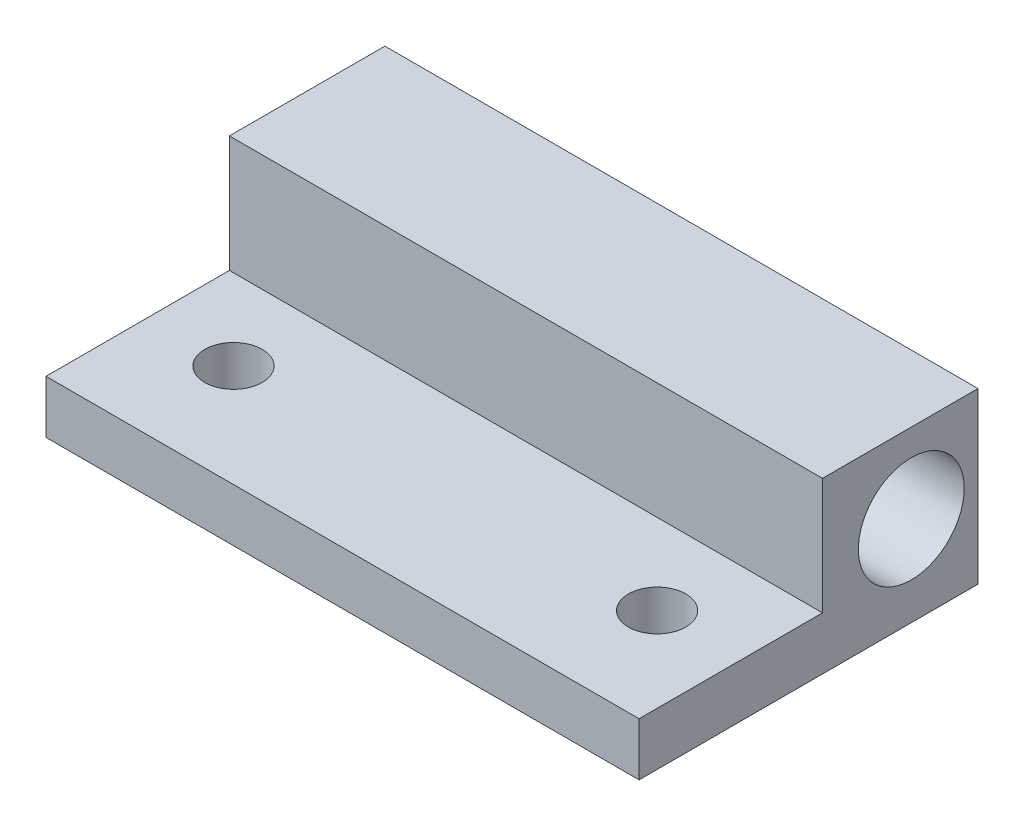
SolidWorks part; units mm, degrees
ref_plane "Front Plane" through (0, 0, 0) normal (0, 0, 1) x (1, 0, 0)
ref_plane "Top Plane" through (0, 0, 0) normal (0, 1, 0) x (1, 0, 0)
ref_plane "Right Plane" through (0, 0, 0) normal (1, 0, 0) x (0, 0, -1)
sketch "Sketch1" plane through (0, 0, 0) normal (0, 1, 0) x (1, 0, 0)
  line L1 (-56.6952, -19.5426) -> (-12.2452, -19.5426)
  line L2 (-56.6952, -19.5426) -> (-56.6952, -44.9426)
  line L3 (-56.6952, -44.9426) -> (-12.2452, -44.9426)
  line L4 (-12.2452, -19.5426) -> (-12.2452, -44.9426)
  dimension "D1" = 25.4
  dimension "D2" = 44.45
extrude "Boss-Extrude1" add sketch "Sketch1" along normal blind 12.7
sketch "Sketch2" plane through (-12.2452, 0, 0) normal (1, 0, 0) x (0, 0, -1)
  line L0 (-44.9426, 0) -> (-19.5426, 0) construction
  line L1 (-44.9426, 12.7) -> (-44.9426, 0) construction
  circle A0 centre (-24.5435, 6.7469) radius 3.9688
  dimension "D1" = 7.9375
  dimension "D2" = 6.7469
  dimension "D3" = 20.3991
extrude "Cut-Extrude1" cut sketch "Sketch2" against normal up to next
hole_wizard "#18 (0.1695) Diameter Hole1" positions "Sketch4" profile "Sketch3" hole size "#18" standard "Ansi Inch" end condition up to next
sketch "Sketch4" plane through (0, 12.7, 0) normal (0, 1, 0) x (-1, 0, 0)
  line L0 (56.6952, 44.9426) -> (12.2452, 44.9426) construction
  line L1 (56.6952, 19.5426) -> (56.6952, 44.9426) construction
  point P0 (50.3452, 37.2435)
  point P1 (18.5952, 37.2435)
  dimension "D1" = 7.6991
  dimension "D2" = 31.75
  dimension "D3" = 6.35
  dimension "D4" = 7.6991
sketch "Sketch3" plane through (-50.3452, 12.7, 37.2435) normal (1, 0, 0) x (0, 0, 1)
  line L0 (0, 0) -> (0, 12.7)
  line L1 (0, 12.7) -> (2.1526, 12.7)
  line L2 (2.1526, 12.7) -> (2.1526, 0)
  line L5 (2.1526, 0) -> (0, 0)
  line L11 (0, -6.35) -> (0, 107.95) construction
  dimension "Thru Hole Dia." = 4.3053
  dimension "Thru Hole Depth" = 12.7
sketch "Sketch5" plane through (0, 12.7, 0) normal (0, 1, 0) x (1, 0, 0)
  line L0 (-56.6952, -19.5426) -> (-56.6952, -44.9426) construction
  line L1 (-12.2452, -44.9426) -> (-56.6952, -44.9426)
  line L2 (-12.2452, -44.9426) -> (-12.2452, -31.1971)
  line L3 (-12.2452, -31.1971) -> (-56.6952, -31.1971)
  line L4 (-56.6952, -44.9426) -> (-56.6952, -31.1971)
extrude "Cut-Extrude2" cut sketch "Sketch5" against normal blind 8.7312
equation "\"D1@Sketch4\" = \"D3@Sketch2\"-.5"
equation "\"D3@Sketch4\" = (\"D2@Sketch1\"-\"D2@Sketch4\")/2"
equation "\"D4@Sketch4\" = \"D1@Sketch4\""
